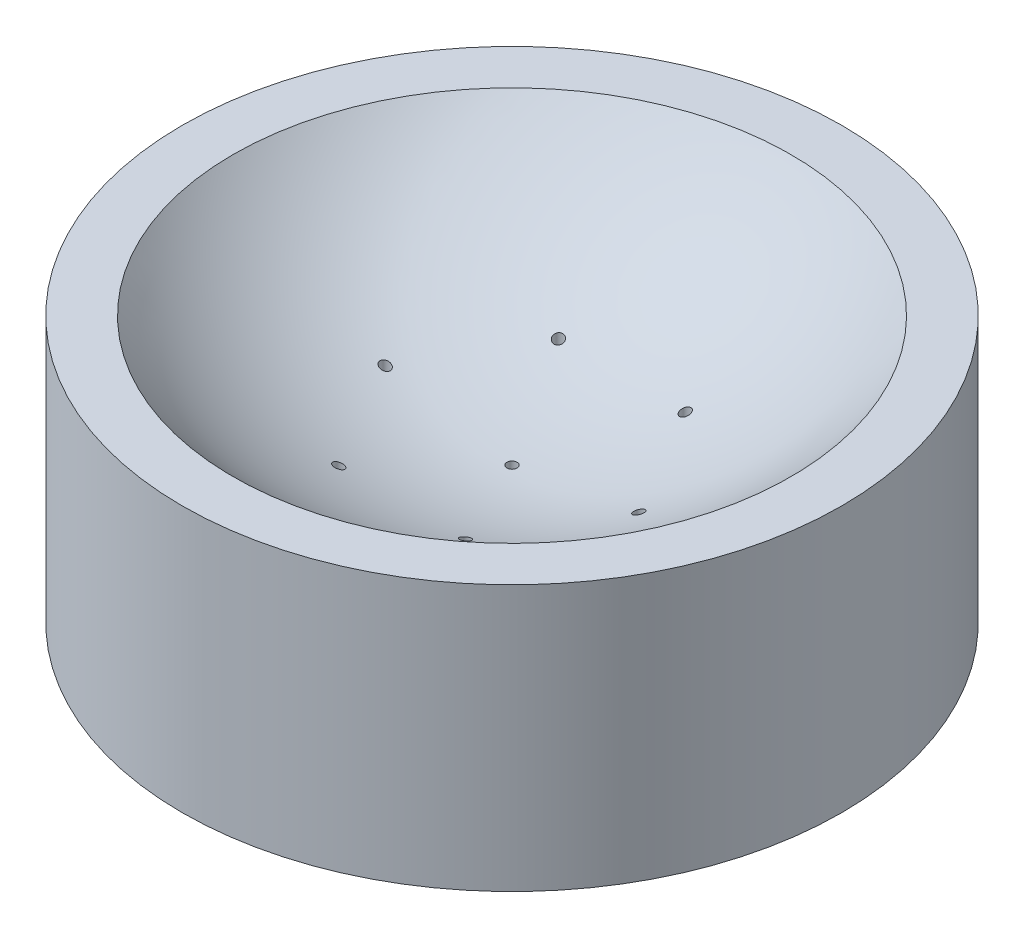
SolidWorks part; units mm, degrees
material "ABS"
ref_plane "Front Plane" through (0, 0, 0) normal (0, 0, 1) x (1, 0, 0)
ref_plane "Top Plane" through (0, 0, 0) normal (0, 1, 0) x (1, 0, 0)
ref_plane "Right Plane" through (0, 0, 0) normal (1, 0, 0) x (0, 0, -1)
sketch "Sketch2" plane through (0, 0, 0) normal (0, 0, 1) x (1, 0, 0)
  line L0 (0, -72) -> (0, -88.8458)
  line L1 (-55, -46.465) -> (-65, -46.465)
  line L2 (-55, -88.8458) -> (0, -88.8458)
  line L4 (-55, -88.8458) -> (-65, -88.8458)
  line L6 (-65, -88.8458) -> (-65, -46.465)
  arc A2 (-55, -46.465) -> (0, -72) centre (0, 0) ccw
revolve "Revolve1" add sketch "Sketch2" angle 360 about L0
sketch "Sketch4" plane through (0, -88.8458, 0) normal (0, -1, 0) x (1, 0, 0)
  line L1 (23.3094, 0) -> (-23.3094, 0) construction
  circle A0 centre (0, 0) radius 1
  circle A1 centre (25, 0) radius 1
  circle A2 centre (12.5, -21.6506) radius 1
  circle A3 centre (-12.5, -21.6506) radius 1
  circle A4 centre (-25, 0) radius 1
  circle A5 centre (-12.5, 21.6506) radius 1
  circle A6 centre (12.5, 21.6506) radius 1
  point P20 (0, 0)
extrude "Cut-Extrude3" cut sketch "Sketch4" against normal through all
sketch "Sketch6" plane through (0, -88.8458, 0) normal (0, -1, 0) x (1, 0, 0)
  circle A0 centre (0, 0) radius 55
  circle A2 centre (0, 0) radius 65
extrude "Boss-Extrude1" add sketch "Sketch6" along normal blind 10
